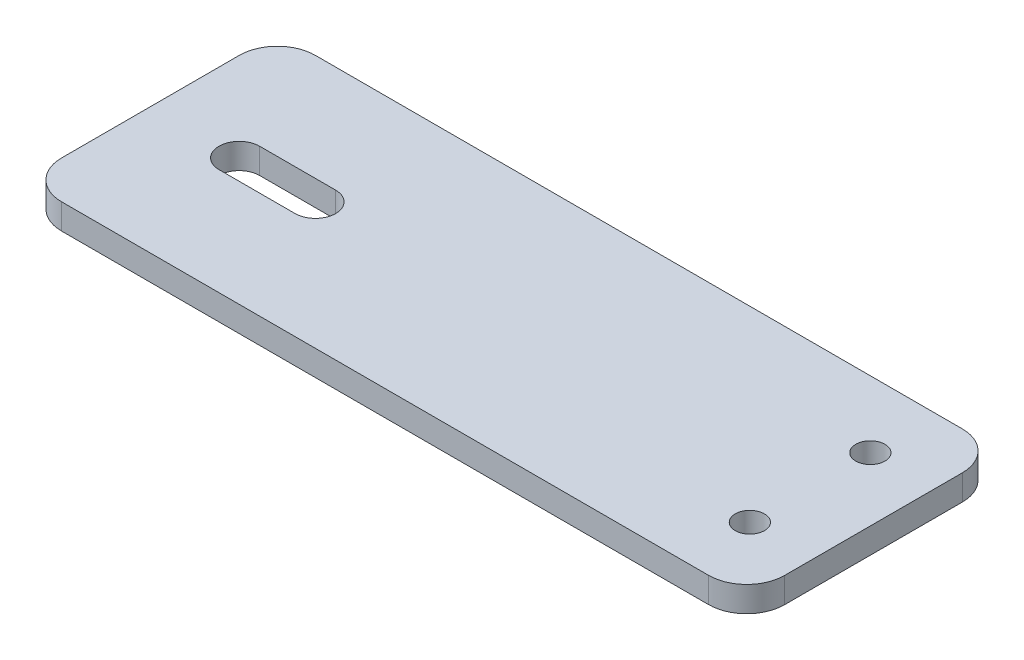
SolidWorks part; units mm, degrees
material "E-玻璃纤维"
ref_plane "前视基准面" through (0, 0, 0) normal (0, 0, 1) x (1, 0, 0)
ref_plane "上视基准面" through (0, 0, 0) normal (0, 1, 0) x (1, 0, 0)
ref_plane "右视基准面" through (0, 0, 0) normal (1, 0, 0) x (0, 0, -1)
sketch "草图1" plane through (0, 0, 0) normal (0, 1, 0) x (1, 0, 0)
  line L0 (0, 0) -> (46.2325, 0) construction
  line L1 (-10, 10) -> (10, 10)
  line L2 (-10, 10) -> (-10, -10)
  line L3 (-10, -10) -> (10, -10)
  line L5 (-10, 10) -> (10, -10) construction
  line L6 (-10, -10) -> (10, 10) construction
  line L7 (10, 10) -> (10, -10) construction
  line L8 (10, 10) -> (47, 10)
  line L10 (10, -10) -> (47, -10)
  line L11 (47, 10) -> (47, -10)
  circle A0 centre (0, 0) radius 1.6
  circle A5 centre (42, -4.75) radius 1.15
  circle A6 centre (42, 4.75) radius 1.15
  point P0 (0, 0)
  dimension "D1" = 3.2
  dimension "D4" = 9.5
  dimension "D5" = 2.3
  dimension "D2" = 20
  dimension "D3" = 20
  dimension "D6" = 32
  dimension "D7" = 5
extrude "凸台-拉伸1" add sketch "草图1" along normal blind 2
fillet "圆角2" radius 3 4 edges at (-10, 1, -10) (-10, 1, 10) (47, 1, -10) (47, 1, 10)
sketch "草图2" plane through (0, 0, 0) normal (0, -1, 0) x (1, 0, 0)
  line L0 (-3, 0) -> (3, 0) construction
  line L1 (-3, 1.6) -> (3, 1.6)
  line L2 (-3, -1.6) -> (3, -1.6)
  arc A0 (-3, 1.6) -> (-3, -1.6) centre (-3, 0) ccw
  arc A1 (3, -1.6) -> (3, 1.6) centre (3, 0) ccw
  point P2 (0, 0)
  dimension "D1" = 3.2
  dimension "D2" = 6
extrude "切除-拉伸1" cut sketch "草图2" against normal blind 10
